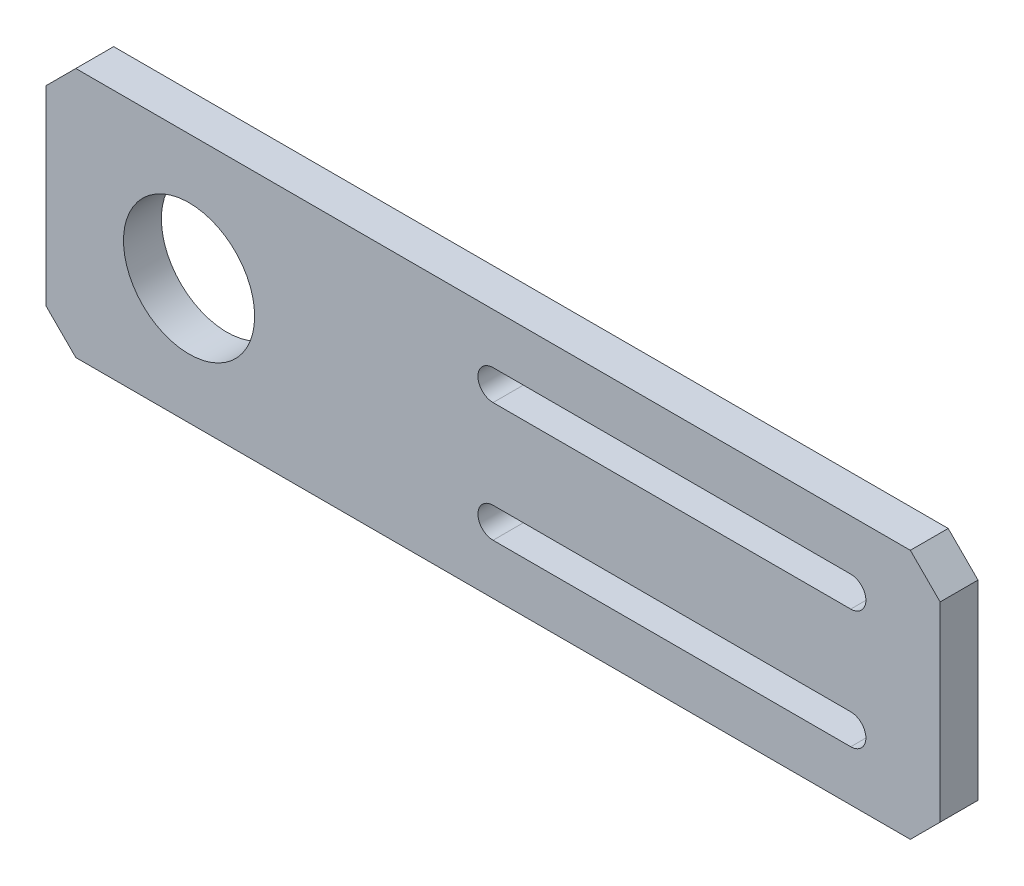
SolidWorks part; units mm, degrees
ref_plane "Front Plane" through (0, 0, 0) normal (0, 0, 1) x (1, 0, 0)
ref_plane "Top Plane" through (0, 0, 0) normal (0, 1, 0) x (1, 0, 0)
ref_plane "Right Plane" through (0, 0, 0) normal (1, 0, 0) x (0, 0, -1)
sketch "Sketch1" plane through (0, 0, 0) normal (0, 0, 1) x (1, 0, 0)
  line L1 (-102.5, 21) -> (102.5, 21)
  line L2 (-102.5, 21) -> (-102.5, -21)
  line L3 (-102.5, -21) -> (102.5, -21)
  line L4 (102.5, 21) -> (102.5, -21)
  line L5 (-102.5, 21) -> (102.5, -21) construction
  line L6 (-102.5, -21) -> (102.5, 21) construction
  point P0 (0, 0)
  dimension "D1" = 205
  dimension "D2" = 42
extrude "Boss-Extrude1" add sketch "Sketch1" along normal blind 6.35
sketch "Sketch3" plane through (0, 0, 6.35) normal (0, 0, 1) x (1, 0, 0)
  line L0 (-62.5, 10) -> (-62.5, -10) construction
  line L1 (-102.5, 21) -> (-102.5, -21) construction
  circle A0 centre (-62.5, 10) radius 2
  circle A1 centre (-62.5, -10) radius 2
  point P4 (-62.5, 0)
  dimension "D1" = 4
  dimension "D2" = 20
  dimension "D3" = 40
sketch "Sketch4" plane through (0, 0, 6.35) normal (0, 0, 1) x (1, 0, 0)
  line L0 (-102.5, 21) -> (-102.5, -21) construction
  line L1 (102.5, -21) -> (102.5, 21) construction
  circle A0 centre (-78.5, 0) radius 11
  circle A1 centre (82.5, 0) radius 11 construction
  dimension "D2" = 22
  dimension "D3" = 20
  dimension "D1" = 24
  dimension "D4" = 161
extrude "Cut-Extrude3" cut sketch "Sketch4" against normal through all
chamfer "Chamfer1" distance 5 angle 45 4 edges at (-102.5, 21, 3.175) (-102.5, -21, 3.175) (102.5, 21, 3.175) (102.5, -21, 3.175)
sketch "Sketch5" plane through (0, 0, 6.35) normal (0, 0, 1) x (1, 0, 0)
  line L0 (102.5, -16) -> (102.5, 16) construction
  circle A0 centre (79.5, 0) radius 11
  dimension "D1" = 22
  dimension "D2" = 23
extrude "Cut-Extrude4" cut sketch "Sketch5" against normal blind 25
sketch "Sketch7" plane through (0, 0, 6.35) normal (0, 0, 1) x (1, 0, 0)
  line L4 (7.5, 3.175) -> (-7.5, 3.175)
  line L5 (7.5, -3.175) -> (7.5, 3.175)
  line L6 (-7.5, -3.175) -> (7.5, -3.175)
  line L7 (-7.5, 3.175) -> (-7.5, -3.175)
  line L8 (7.5, 3.175) -> (-7.5, 3.175)
  line L9 (7.5, -3.175) -> (7.5, 3.175)
  line L10 (-7.5, -3.175) -> (7.5, -3.175)
  line L11 (-7.5, 3.175) -> (-7.5, -3.175)
  dimension "D1" = 0
sketch "Sketch8" [suppressed] plane through (0, 0, 6.35) normal (0, 0, 1) x (1, 0, 0)
  line L4 (25.5, 3.175) -> (10.5, 3.175)
  line L5 (10.5, 3.175) -> (10.5, -3.175)
  line L6 (10.5, -3.175) -> (25.5, -3.175)
  line L7 (25.5, -3.175) -> (25.5, 3.175)
  line L8 (25.5, 3.175) -> (10.5, 3.175)
  line L9 (10.5, 3.175) -> (10.5, -3.175)
  line L10 (10.5, -3.175) -> (25.5, -3.175)
  line L11 (25.5, -3.175) -> (25.5, 3.175)
  dimension "D1" = 0
extrude "Cut-Extrude7" [suppressed] cut sketch "Sketch8" against normal through all
sketch "Sketch9" [suppressed] plane through (0, 0, 6.35) normal (0, 0, 1) x (1, 0, 0)
  circle A0 centre (80, 0) radius 11 construction
  circle A1 centre (80, 0) radius 11
extrude "Cut-Extrude8" [suppressed] cut sketch "Sketch9" against normal through all
sketch "Sketch10" [suppressed] plane through (0, 0, 6.35) normal (0, 0, 1) x (1, 0, 0)
  circle A0 centre (80, 0) radius 15
  dimension "D1" = 25
extrude "Cut-Extrude9" [suppressed] cut sketch "Sketch10" against normal through all
sketch "Sketch11" [suppressed] plane through (0, 0, 6.35) normal (0, 0, 1) x (1, 0, 0)
  circle A0 centre (95.5563, 15.5563) radius 1.5 construction
  circle A1 centre (64.4437, 15.5563) radius 1.5 construction
  circle A2 centre (95.5563, -15.5563) radius 1.5 construction
  circle A3 centre (64.4437, -15.5563) radius 1.5 construction
  circle A4 centre (95.5563, 15.5563) radius 1.5
  circle A5 centre (64.4437, 15.5563) radius 1.5
  circle A6 centre (95.5563, -15.5563) radius 1.5
  circle A7 centre (64.4437, -15.5563) radius 1.5
extrude "Cut-Extrude10" [suppressed] cut sketch "Sketch11" against normal through all
sketch "Sketch12" [suppressed] plane through (0, 0, 6.35) normal (0, 0, 1) x (1, 0, 0)
  line L0 (-100, 16) -> (-100, -16) construction
  circle A0 centre (-93, 0) radius 3.302
  point P4 (-100, 0)
  dimension "D1" = 6.604
  dimension "D2" = 7
extrude "Cut-Extrude11" [suppressed] cut sketch "Sketch12" against normal through all
sketch "Sketch13" plane through (0, 0, 6.35) normal (0, 0, 1) x (1, 0, 0)
  line L0 (47.5, 16) -> (47.5, -16)
  line L1 (42.5, 21) -> (47.5, 16)
  line L2 (47.5, -16) -> (42.5, -21)
  line L3 (97.5, 21) -> (-97.5, 21) construction
  line L4 (-97.5, -21) -> (97.5, -21) construction
  line L5 (97.5, 21) -> (-97.5, 21)
  line L6 (-97.5, -21) -> (97.5, -21)
  line L7 (-27.5, 10) -> (32.5, 10) construction
  line L8 (97.5, 21) -> (-97.5, 21)
  line L9 (-97.5, 21) -> (-102.5, 16)
  line L10 (-102.5, 16) -> (-102.5, -16)
  line L11 (-102.5, -16) -> (-97.5, -21)
  line L12 (-97.5, -21) -> (97.5, -21)
  line L13 (97.5, -21) -> (102.5, -16)
  line L14 (102.5, -16) -> (102.5, 16)
  line L15 (102.5, 16) -> (97.5, 21)
  line L16 (42.5, 21) -> (-97.5, 21)
  line L17 (-97.5, 21) -> (-102.5, 16)
  line L18 (-102.5, 16) -> (-102.5, -16)
  line L19 (-102.5, -16) -> (-97.5, -21)
  line L20 (-97.5, -21) -> (42.5, -21)
  line L21 (97.5, -21) -> (102.5, -16)
  line L22 (102.5, -16) -> (102.5, 16)
  line L23 (102.5, 16) -> (97.5, 21)
  line L24 (-27.5, 12.54) -> (32.5, 12.54)
  line L25 (-27.5, 7.46) -> (32.5, 7.46)
  line L26 (0, 0) -> (47.5, 0) construction
  line L27 (-27.5, -10) -> (32.5, -10) construction
  line L28 (-27.5, -12.54) -> (32.5, -12.54)
  line L29 (-27.5, -7.46) -> (32.5, -7.46)
  arc A0 (-27.5, 12.54) -> (-27.5, 7.46) centre (-27.5, 10) ccw
  arc A1 (32.5, 7.46) -> (32.5, 12.54) centre (32.5, 10) ccw
  arc A2 (-27.5, -12.54) -> (-27.5, -7.46) centre (-27.5, -10) cw
  arc A3 (32.5, -7.46) -> (32.5, -12.54) centre (32.5, -10) cw
  point P2 (47.5, 21)
  point P9 (47.5, -21)
  point P16 (2.5, 10)
  point P27 (2.5, -10)
  circle M18 centre (79.5, 0) radius 11
  line M20 (97.5, 21) -> (-97.5, 21)
  line M24 (-97.5, -21) -> (97.5, -21)
  line M25 (97.5, -21) -> (102.5, -16)
  line M26 (102.5, -16) -> (102.5, 16)
  line M27 (102.5, 16) -> (97.5, 21)
  dimension "D7" = 2.54
  dimension "D2" = 150
  dimension "D3" = 60
  dimension "D4" = 15
  dimension "D8" = 10
  dimension "D1" = 0
extrude "Cut-Extrude12" cut sketch "Sketch13" against normal blind 10 contours L0 L2 L1 M24 M25 M26 M27 M20 M18 | L25 A1 L24 A0 | A3 L29 A2 L28
